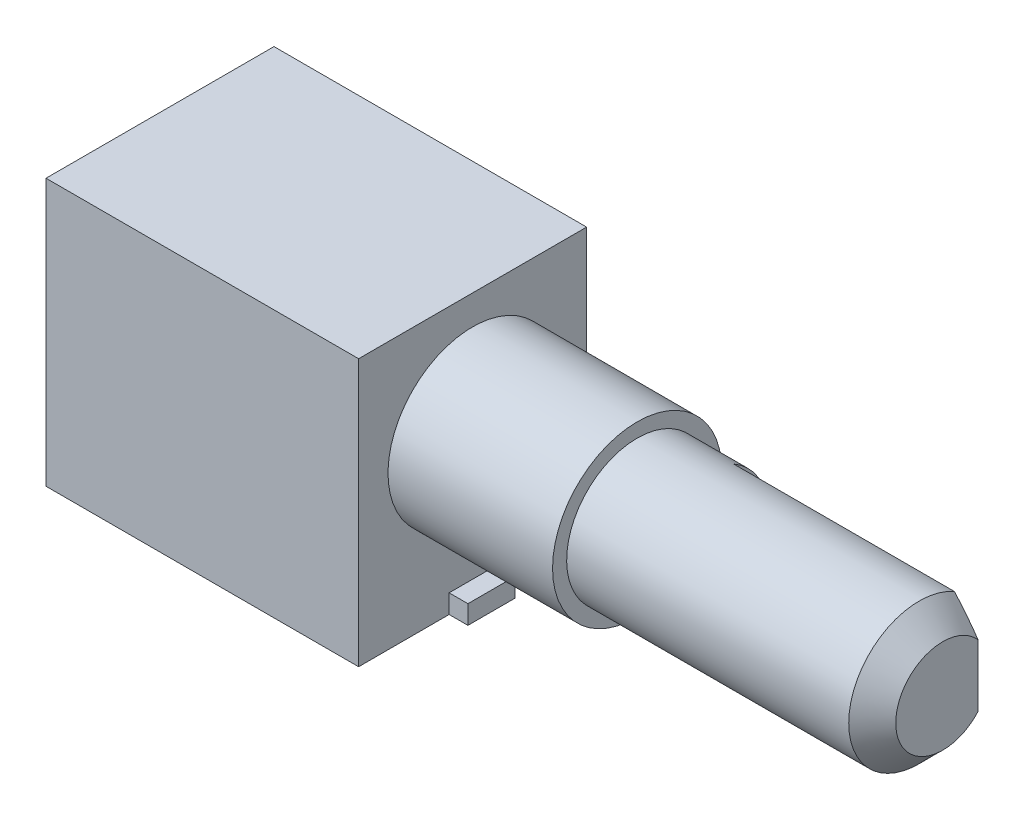
SolidWorks part; units mm, degrees
ref_plane "Front Plane" through (0, 0, 0) normal (0, 0, 1) x (1, 0, 0)
ref_plane "Top Plane" through (0, 0, 0) normal (0, 1, 0) x (1, 0, 0)
ref_plane "Right Plane" through (0, 0, 0) normal (1, 0, 0) x (0, 0, -1)
sketch "Sketch1" plane through (0, 0, 0) normal (0, 0, 1) x (1, 0, 0)
  line L1 (0, 0) -> (13.3, 0)
  line L2 (0, 0) -> (0, 11.35)
  line L3 (0, 11.35) -> (13.3, 11.35)
  line L4 (13.3, 0) -> (13.3, 11.35)
  dimension "D1" = 13.3
  dimension "D2" = 11.35
extrude "Boss-Extrude1" add sketch "Sketch1" along normal blind 9.7
sketch "Sketch2" plane through (13.3, 0, 0) normal (1, 0, 0) x (0, 0, -1)
  line L0 (-9.7, 0) -> (0, 0) construction
  circle A0 centre (-4.85, 6.5) radius 3.6
  dimension "D2" = 7.2
  dimension "D1" = 6.5
extrude "Boss-Extrude2" add sketch "Sketch2" along normal blind 7
sketch "Sketch3" plane through (20.3, 0, 0) normal (1, 0, 0) x (0, 0, -1)
  circle A0 centre (-4.85, 6.5) radius 3
  dimension "D1" = 6
extrude "Boss-Extrude4" add sketch "Sketch3" along normal offset from surface (13 mm away) 20 up to face at (13.3, 5.675, 4.85) offset beyond the face yes
sketch "Sketch4" plane through (13.3, 0, 0) normal (1, 0, 0) x (0, 0, -1)
  line L0 (-9.7, 0) -> (0, 0) construction
  line L1 (-5.85, 0) -> (-3.85, 0)
  line L2 (-5.85, 0) -> (-5.85, 0.8)
  line L3 (-5.85, 0.8) -> (-3.85, 0.8)
  line L4 (-3.85, 0) -> (-3.85, 0.8)
  point P6 (-4.85, 0.8)
  point P7 (-4.85, 0)
  dimension "D1" = 2
  dimension "D2" = 0.8
extrude "Boss-Extrude5" add sketch "Sketch4" along normal blind 0.8
ref_plane "Plane1" through (0, 0, 4.85) normal (0, 0, 1) x (1, 0, 0)
sketch "Sketch5" plane through (33.3, 0, 0) normal (1, 0, 0) x (0, 0, -1)
  line L0 (-4.85, 6.5) -> (-3.35, 6.5) construction
  line L1 (-3.35, 11.0315) -> (6.2958, 11.0315)
  line L2 (-3.35, 11.0315) -> (-3.35, 1.9685)
  line L3 (-3.35, 1.9685) -> (6.2958, 1.9685)
  line L4 (6.2958, 11.0315) -> (6.2958, 1.9685)
  line L5 (-3.35, 11.0315) -> (6.2958, 1.9685) construction
  line L6 (-3.35, 1.9685) -> (6.2958, 11.0315) construction
  line L7 (-7.85, 9.0779) -> (-7.85, 4.2547) construction
  circle A0 centre (-4.85, 6.5) radius 3 construction
  point P0 (1.4729, 6.5)
  dimension "D1" = 4.5
extrude "Cut-Extrude1" cut sketch "Sketch5" against normal blind 10.4
chamfer "Chamfer1" distance 1 angle 45 1 edges at (33.3, 6.5, 7.85)
